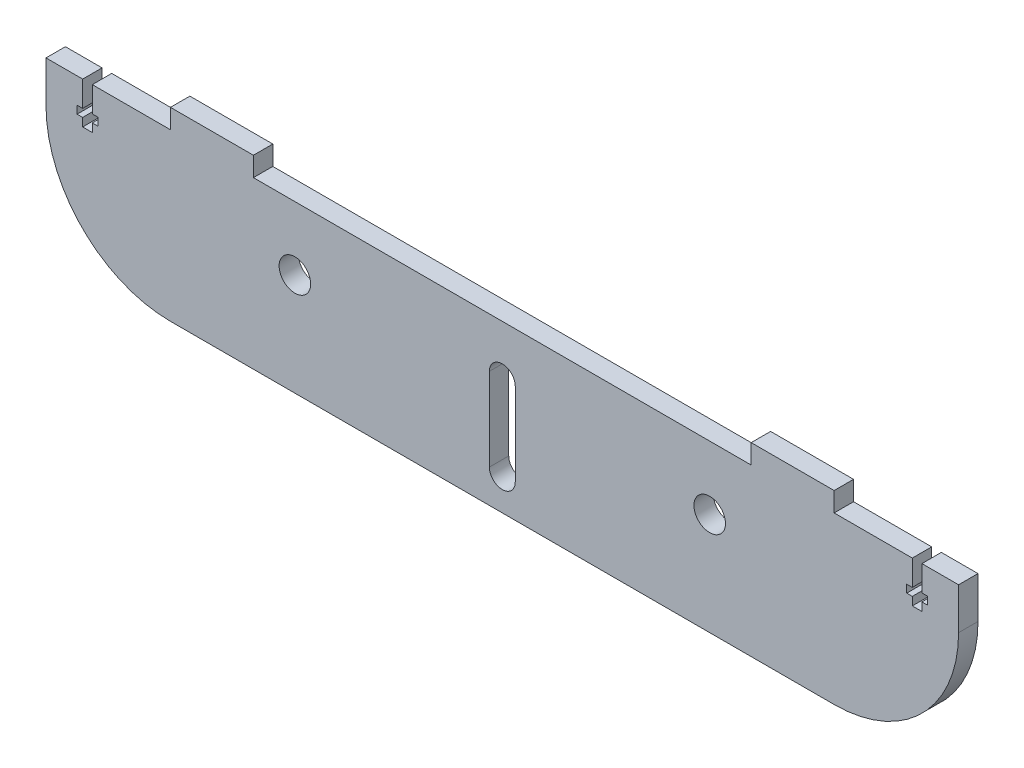
SolidWorks part; units mm, degrees
ref_plane "Front Plane" through (0, 0, 0) normal (0, 0, 1) x (1, 0, 0)
ref_plane "Top Plane" through (0, 0, 0) normal (0, 1, 0) x (1, 0, 0)
ref_plane "Right Plane" through (0, 0, 0) normal (1, 0, 0) x (0, 0, -1)
sketch "Sketch1" plane through (0, 0, 0) normal (0, 0, 1) x (1, 0, 0)
  line L0 (-101.6, 25.4) -> (-101.6, 31.3436)
  line L1 (-139.7, 25.4) -> (-101.6, 25.4)
  line L2 (-139.7, 25.4) -> (-139.7, -25.4)
  line L3 (-139.7, -25.4) -> (139.7, -25.4)
  line L4 (139.7, 25.4) -> (139.7, -25.4)
  line L5 (-139.7, 25.4) -> (139.7, -25.4) construction
  line L6 (-139.7, -25.4) -> (139.7, 25.4) construction
  line L7 (-101.6, 31.3436) -> (-76.2, 31.3436)
  line L8 (-76.2, 31.3436) -> (-76.2, 25.4)
  line L9 (-76.2, 25.4) -> (76.2, 25.4)
  line L10 (0, 60.3217) -> (0, -57.4102) construction
  line L11 (76.2, 31.3436) -> (76.2, 25.4)
  line L12 (101.6, 31.3436) -> (76.2, 31.3436)
  line L13 (101.6, 25.4) -> (101.6, 31.3436)
  line L14 (101.6, 25.4) -> (139.7, 25.4)
  point P0 (0, 0)
  dimension "D1" = 279.4
  dimension "D2" = 50.8
  dimension "D3" = 25.4
  dimension "D4" = 5.9436
  dimension "D5" = 76.2
extrude "Boss-Extrude1" add sketch "Sketch1" along normal blind 5.9436
sketch "Sketch2" plane through (0, 0, 5.9436) normal (0, 0, 1) x (1, 0, 0)
  line L0 (-128.4732, 25.4) -> (-128.4732, 17.6212)
  line L1 (-101.6, 25.4) -> (-139.7, 25.4) construction
  line L2 (-128.4732, 17.6212) -> (-130.175, 17.6212)
  line L3 (-130.175, 17.6212) -> (-130.175, 15.24)
  line L4 (-130.175, 15.24) -> (-128.4732, 15.24)
  line L5 (-128.4732, 15.24) -> (-128.4732, 12.7)
  line L6 (-128.4732, 12.7) -> (-125.5268, 12.7)
  line L7 (-125.5268, 12.7) -> (-125.5268, 15.24)
  line L8 (-125.5268, 15.24) -> (-123.825, 15.24)
  line L9 (-123.825, 15.24) -> (-123.825, 17.6212)
  line L10 (-123.825, 17.6212) -> (-125.5268, 17.6212)
  line L11 (-125.5268, 17.6212) -> (-125.5268, 25.4)
  line L12 (-127, 12.7) -> (-127, 23.6811) construction
  line L13 (-139.7, 25.4) -> (-139.7, -25.4) construction
  line L14 (0, 37.1191) -> (0, -25.8621) construction
  line L15 (127, 12.7) -> (127, 23.6811) construction
  line L16 (125.5268, 17.6212) -> (125.5268, 25.4)
  line L17 (123.825, 17.6212) -> (125.5268, 17.6212)
  line L18 (123.825, 15.24) -> (123.825, 17.6212)
  line L19 (125.5268, 15.24) -> (123.825, 15.24)
  line L20 (125.5268, 12.7) -> (125.5268, 15.24)
  line L21 (128.4732, 12.7) -> (125.5268, 12.7)
  line L22 (128.4732, 15.24) -> (128.4732, 12.7)
  line L23 (130.175, 15.24) -> (128.4732, 15.24)
  line L24 (130.175, 17.6212) -> (130.175, 15.24)
  line L25 (128.4732, 17.6212) -> (130.175, 17.6212)
  line L26 (128.4732, 25.4) -> (128.4732, 17.6212)
  line L27 (-128.4732, 25.4) -> (-125.5268, 25.4)
  line L28 (125.5268, 25.4) -> (128.4732, 25.4)
  dimension "D1" = 2.3813
  dimension "D2" = 12.7
  dimension "D3" = 2.54
  dimension "D4" = 6.35
  dimension "D5" = 2.9464
  dimension "D6" = 12.7
extrude "Cut-Extrude1" cut sketch "Sketch2" against normal blind 6.35
sketch "Sketch3" plane through (0, 0, 0) normal (0, 0, -1) x (-1, 0, 0)
  line L0 (0, 25.4) -> (0, -25.4) construction
  line L1 (-76.2, 25.4) -> (76.2, 25.4) construction
  line L2 (139.7, -25.4) -> (-139.7, -25.4) construction
  line L3 (-76.2, 25.4) -> (76.2, 25.4) construction
  line L4 (-139.7, -25.4) -> (-139.7, 25.4) construction
  line L7 (3.9688, 10.16) -> (3.9688, -15.24)
  line L8 (-3.9687, 10.16) -> (-3.9687, -15.24)
  circle A0 centre (-63.5, 5.9436) radius 4.826
  circle A1 centre (63.5, 5.9436) radius 4.826
  arc A2 (-3.9687, -15.24) -> (3.9688, -15.24) centre (0, -15.24) ccw
  arc A3 (3.9688, 10.16) -> (-3.9687, 10.16) centre (0, 10.16) ccw
  point P18 (0, 0)
  point P23 (-139.7, 0)
  dimension "D1" = 9.652
  dimension "D2" = 9.652
  dimension "D3" = 7.9375
  dimension "D4" = 7.9375
  dimension "D5" = 25.4
  dimension "D6" = 15.24
extrude "Cut-Extrude2" cut sketch "Sketch3" against normal through all
sketch "Sketch4" plane through (0, 0, 5.9436) normal (0, 0, 1) x (1, 0, 0)
  line L1 (-101.6, 25.4) -> (-125.5268, 25.4) construction
  line L2 (-139.7, 12.7) -> (-139.7, -25.4)
  line L3 (0, 25.4) -> (0, -25.4) construction
  line L4 (-139.7, -25.4) -> (-101.6, -25.4)
  line L5 (-139.7, 25.4) -> (-139.7, -25.4) construction
  line L6 (139.7, -25.4) -> (101.6, -25.4)
  line L7 (76.2, 25.4) -> (-76.2, 25.4) construction
  line L8 (-139.7, -25.4) -> (139.7, -25.4) construction
  line L9 (139.7, 12.7) -> (139.7, -25.4)
  arc A0 (-139.7, 12.7) -> (-101.6, -25.4) centre (-101.6, 12.7) ccw
  arc A1 (139.7, 12.7) -> (101.6, -25.4) centre (101.6, 12.7) cw
  point P16 (-113.5634, 25.4)
  dimension "D1" = 50.8
extrude "Cut-Extrude3" cut sketch "Sketch4" against normal through all contours L2 L4 A0
